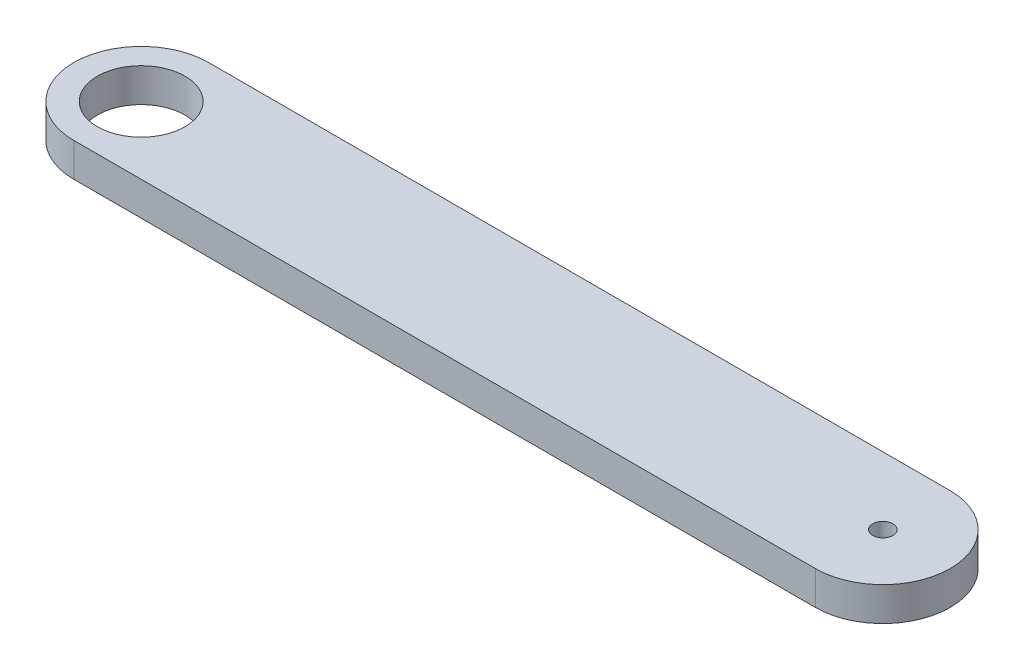
SolidWorks part; units mm, degrees
ref_plane "Front Plane" through (0, 0, 0) normal (0, 0, 1) x (1, 0, 0)
ref_plane "Top Plane" through (0, 0, 0) normal (0, 1, 0) x (1, 0, 0)
ref_plane "Right Plane" through (0, 0, 0) normal (1, 0, 0) x (0, 0, -1)
sketch "Sketch1" plane through (0, 0, 0) normal (0, 1, 0) x (1, 0, 0)
  line L0 (0, 0) -> (220, 0) construction
  line L1 (220, 20) -> (0, 20)
  line L6 (0, -20) -> (220, -20)
  arc A0 (0, 20) -> (0, -20) centre (0, 0) ccw
  arc A1 (220, -20) -> (220, 20) centre (220, 0) ccw
  circle A2 centre (0, 0) radius 13
  circle A3 centre (220, 0) radius 3
  dimension "D3" = 40
  dimension "D6" = 26
  dimension "D7" = 6
  dimension "D1" = 220
extrude "Boss-Extrude1" add sketch "Sketch1" along normal blind 10
